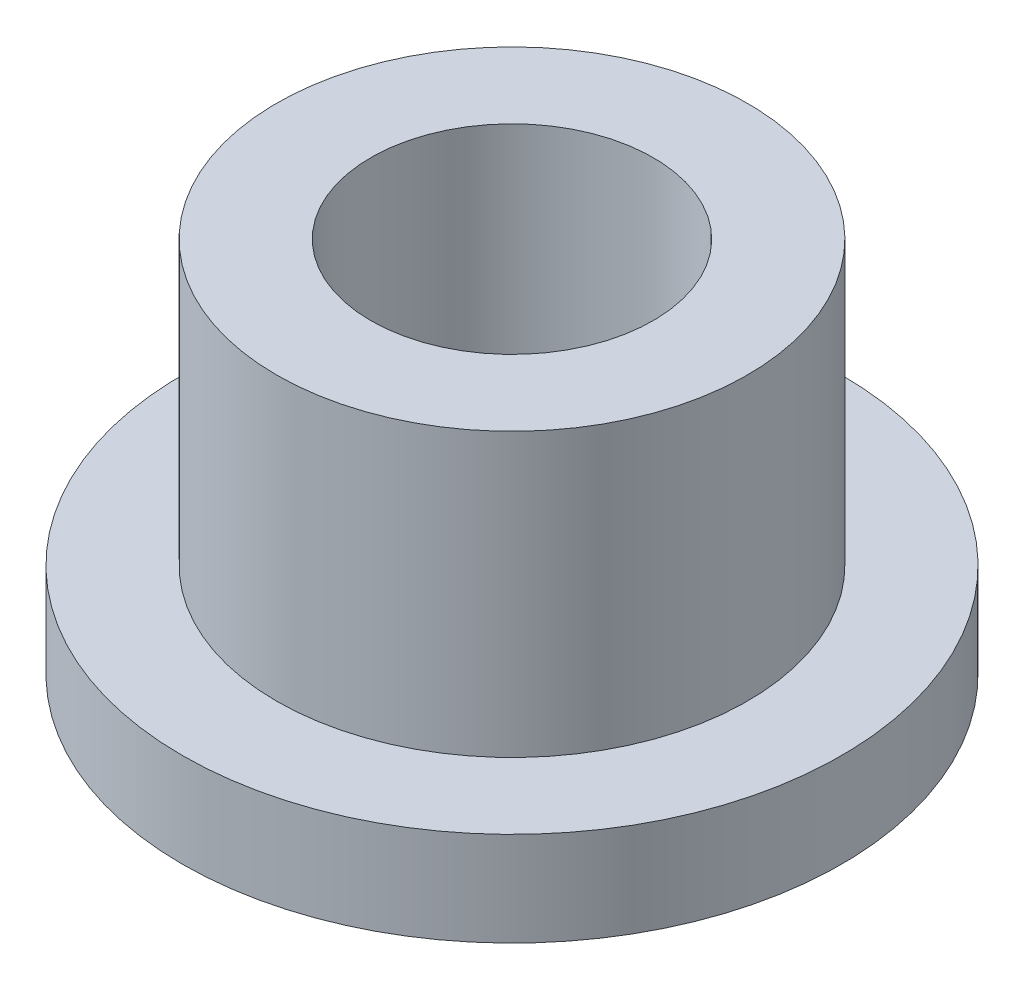
SolidWorks part; units mm, degrees
ref_plane "Front" through (0, 0, 0) normal (0, 0, 1) x (1, 0, 0)
ref_plane "Top" through (0, 0, 0) normal (0, 1, 0) x (1, 0, 0)
ref_plane "Right" through (0, 0, 0) normal (1, 0, 0) x (0, 0, -1)
sketch "Sketch1" plane through (0, 0, 0) normal (0, 1, 0) x (1, 0, 0)
  circle A0 centre (0, 0) radius 2.3813
  circle A1 centre (0, 0) radius 3.9688
  circle A2 centre (0, 0) radius 5.5562
  dimension "ID" = 4.7625
  dimension "OD" = 7.9375
  dimension "FlangeOD" = 11.1125
sketch "Sketch2" plane through (0, 0, 0) normal (0, 1, 0) x (1, 0, 0)
  circle A0 centre (0, 0) radius 2.3813 construction
  circle A1 centre (0, 0) radius 3.9688 construction
  circle A2 centre (0, 0) radius 2.3813
  circle A3 centre (0, 0) radius 3.9688
extrude "Boss-Extrude1" add sketch "Sketch2" along normal blind 6.35
sketch "Sketch3" plane through (0, 0, 0) normal (0, 1, 0) x (1, 0, 0)
  circle A0 centre (0, 0) radius 5.5562 construction
  circle A1 centre (0, 0) radius 3.9688 construction
  circle A2 centre (0, 0) radius 5.5562
  circle A3 centre (0, 0) radius 3.9688
extrude "Boss-Extrude2" add sketch "Sketch3" along normal blind 1.5875
